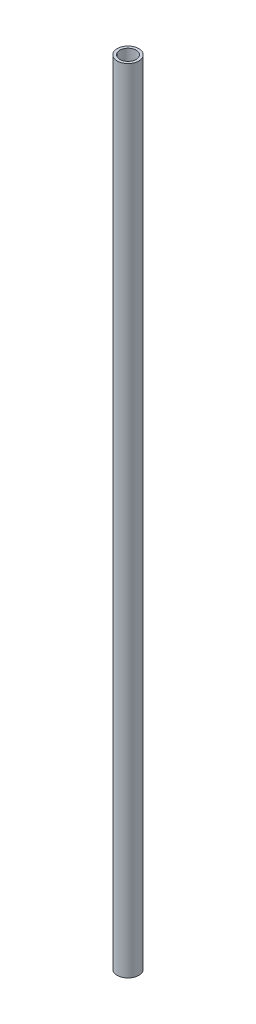
SolidWorks part; units mm, degrees
material "Copper"
ref_plane "Front Plane" through (0, 0, 0) normal (0, 0, 1) x (1, 0, 0)
ref_plane "Top Plane" through (0, 0, 0) normal (0, 1, 0) x (1, 0, 0)
ref_plane "Right Plane" through (0, 0, 0) normal (1, 0, 0) x (0, 0, -1)
sketch "Sketch1" plane through (0, 0, 0) normal (0, 1, 0) x (1, 0, 0)
  circle A0 centre (0, 0) radius 2
  circle A1 centre (0, 0) radius 1.5
  dimension "D1" = 4
  dimension "D2" = 3
extrude "Boss-Extrude1" add sketch "Sketch1" along normal mid plane 147
